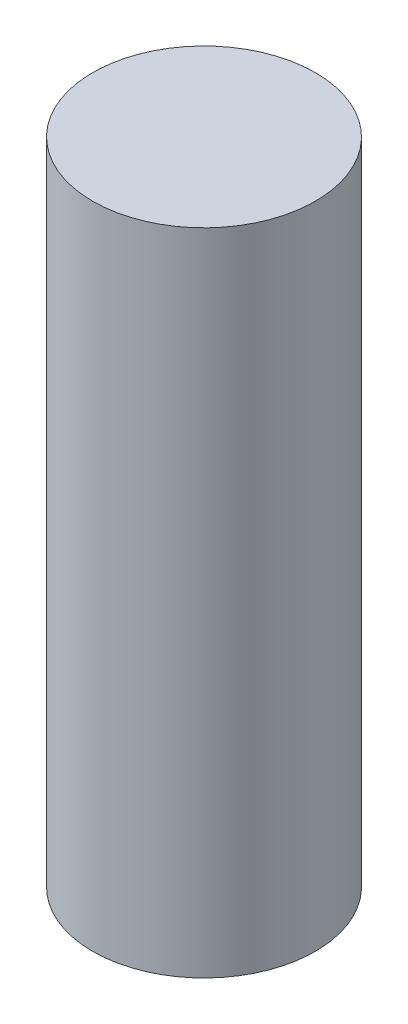
SolidWorks part; units mm, degrees
ref_plane "Front Plane" through (0, 0, 0) normal (0, 0, 1) x (1, 0, 0)
ref_plane "Top Plane" through (0, 0, 0) normal (0, 1, 0) x (1, 0, 0)
ref_plane "Right Plane" through (0, 0, 0) normal (1, 0, 0) x (0, 0, -1)
sketch "Sketch1" plane through (0, 0, 0) normal (0, 1, 0) x (1, 0, 0)
  circle A0 centre (0, 0) radius 3
  dimension "D1" = 6
extrude "Boss-Extrude1" add sketch "Sketch1" along normal blind 17.5
